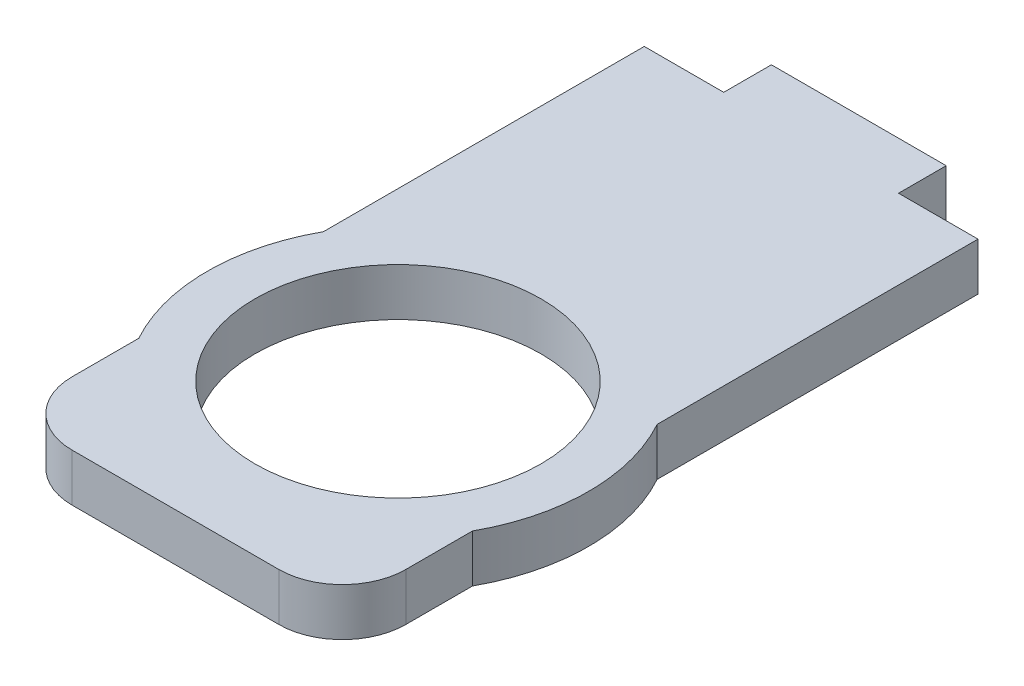
SolidWorks part; units mm, degrees
ref_plane "Alzado" through (0, 0, 0) normal (0, 0, 1) x (1, 0, 0)
ref_plane "Planta" through (0, 0, 0) normal (0, 1, 0) x (1, 0, 0)
ref_plane "Vista lateral" through (0, 0, 0) normal (1, 0, 0) x (0, 0, -1)
sketch "Croquis1" plane through (0, 0, 0) normal (0, 0, 1) x (1, 0, 0)
  line L18 (-30.3351, 49.2179) -> (-30.3351, 46.2179)
  line L19 (-19.3351, 49.2179) -> (-30.3351, 49.2179)
  line L20 (-19.3351, 46.2179) -> (-19.3351, 49.2179)
  line L21 (-30.3351, 46.2179) -> (-19.3351, 46.2179)
  point P0 (-24.8351, 47.7179)
extrude "Saliente-Extruir1" add sketch "Croquis1" against normal up to surface (3 mm away)
sketch "Croquis2" plane through (0, 0, 0) normal (0, 0, 1) x (1, 0, 0)
  line L12 (-14.3351, 46.2179) -> (-14.3351, 49.2179)
  line L13 (-14.3351, 49.2179) -> (-35.3351, 49.2179)
  line L14 (-35.3351, 49.2179) -> (-35.3351, 46.2179)
  line L15 (-35.3351, 46.2179) -> (-14.3351, 46.2179)
  point P0 (-24.8351, 47.7179)
  point P1 (-24.8351, 47.7179)
extrude "Saliente-Extruir2" add sketch "Croquis2" along normal up to surface (40 mm away)
sketch "Croquis3" plane through (0, 46.2179, 0) normal (0, -1, 0) x (1, 0, 0)
  line L0 (-24.8351, 40) -> (-24.8351, 35) construction
  line L1 (-35.3351, 40) -> (-14.3351, 40) construction
  line L2 (-24.8351, 35) -> (-24.8351, 26) construction
  circle A0 centre (-24.8351, 26) radius 9
extrude "Cortar-Extruir1" cut sketch "Croquis3" against normal blind 10
sketch "Croquis4" plane through (0, 46.2179, 0) normal (0, -1, 0) x (-1, 0, 0)
  circle A0 centre (24.8351, -26) radius 12
  circle A1 centre (24.8351, -26) radius 9
extrude "Saliente-Extruir3" add sketch "Croquis4" against normal up to surface (3 mm away) up to face at (-24.8351, 49.2179, 35)
fillet "Redondeo1" radius 4 2 edges at (-35.3351, 47.7179, 40) (-14.3351, 47.7179, 40)
